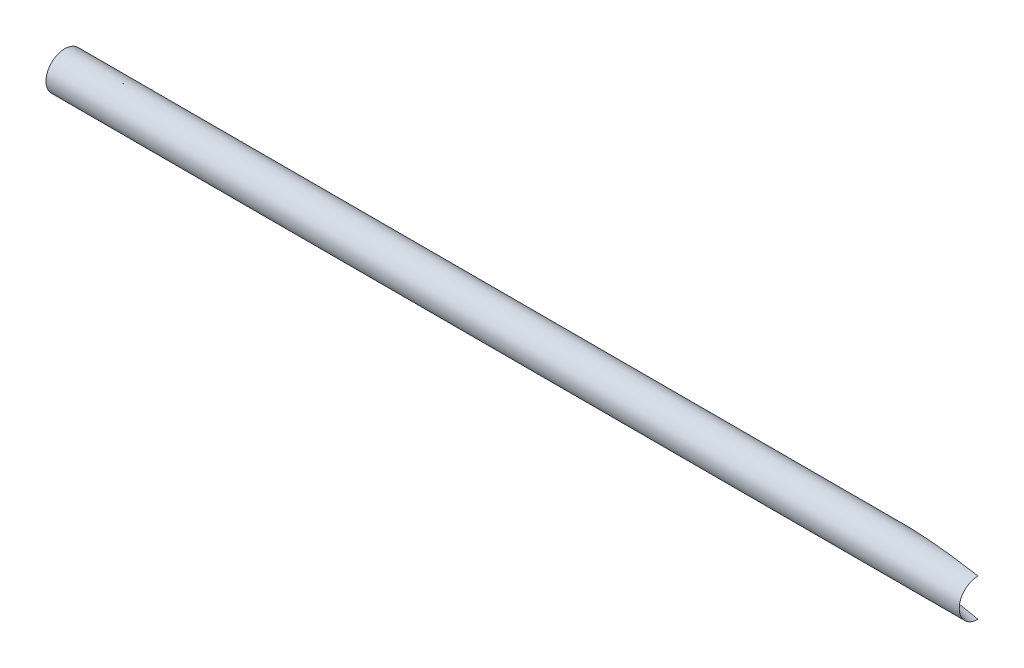
SolidWorks part; units mm, degrees
ref_plane "Front" through (0, 0, 0) normal (0, 0, 1) x (1, 0, 0)
ref_plane "Top" through (0, 0, 0) normal (0, 1, 0) x (1, 0, 0)
ref_plane "Right" through (0, 0, 0) normal (1, 0, 0) x (0, 0, -1)
sketch "Sketch1" plane through (0, 0, 0) normal (0, 0, 1) x (1, 0, 0)
  line L0 (231.775, 0) -> (-231.775, 0)
  point P4 (0, 0)
  dimension "D1" = 463.55
other "Round .75IN X .125IN SIDEWALL(1)"
ref_plane "Plane1" through (231.775, 0, 0) normal (-1, 0, 0) x (0, -1, 0)
sketch "Sketch13" plane through (231.775, 0, 0) normal (-1, 0, 0) x (0, -1, 0)
  circle A0 centre (0, 0) radius 6.35
  circle A1 centre (0, 0) radius 9.525
  point P5 (0, 0)
  dimension "D1" = 19.05
  dimension "D2" = 3.175
sketch "Sketch14" plane through (0, 0, 0) normal (0, 1, 0) x (1, 0, 0)
  line L0 (231.775, 0) -> (0, 70.8607) construction
  line L1 (231.775, -9.525) -> (231.775, 9.525) construction
  line L2 (231.775, 0) -> (-231.775, 0) construction
  line L3 (0, 70.8607) -> (0, 0) construction
  dimension "D1" = 17
ref_plane "Plane2" through (231.775, 0, 0) normal (1, 0, 0) x (0, 0, -1)
sketch "Sketch15" plane through (231.775, 0, 0) normal (1, 0, 0) x (0, 0, -1)
  circle A0 centre (0, 0) radius 6.35 construction
  circle A1 centre (0, 0) radius 9.525
  circle A2 centre (0, 0) radius 9.525
  circle A3 centre (0, 0) radius 6.35
  dimension "D1" = 0
extrude "Cut-Extrude1" cut sketch "Sketch15" along direction (-0.9563, 0, -0.2924) on the side against the normal through all contours M2 | M3 M2
